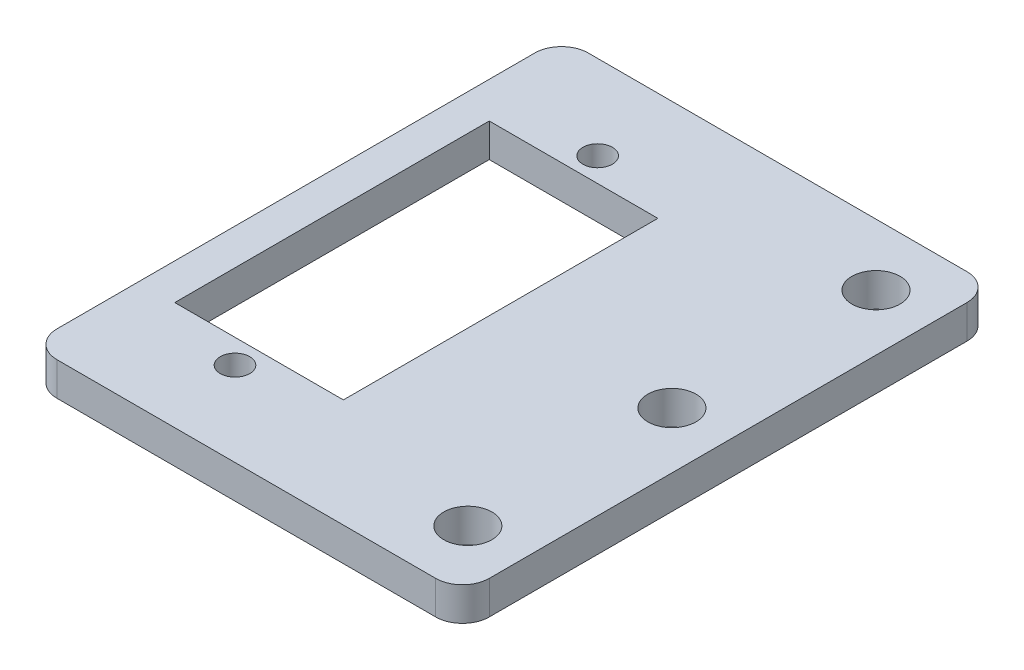
SolidWorks part; units mm, degrees
material "ABS PC"
ref_plane "Front Plane" through (0, 0, 0) normal (0, 0, 1) x (1, 0, 0)
ref_plane "Top Plane" through (0, 0, 0) normal (0, 1, 0) x (1, 0, 0)
ref_plane "Right Plane" through (0, 0, 0) normal (1, 0, 0) x (0, 0, -1)
sketch "Sketch1" plane through (0, 0, 0) normal (0, 1, 0) x (1, 0, 0)
  line L1 (-9, -19.85) -> (23.3, -19.85)
  line L2 (-9, -19.85) -> (-9, 19.85)
  line L3 (-9, 19.85) -> (23.3, 19.85)
  line L4 (23.3, -19.85) -> (23.3, 19.85)
  point P4 (23.3, 0)
  dimension "D1" = 32.3
  dimension "D2" = 39.7
  dimension "D3" = 9
extrude "Plate Size" add sketch "Sketch1" against normal blind 2.5
sketch "Sketch2" plane through (0, 0, 0) normal (0, 1, 0) x (1, 0, 0)
  line L1 (-6.3, -11.75) -> (6.3, -11.75)
  line L2 (-6.3, -11.75) -> (-6.3, 11.75)
  line L3 (-6.3, 11.75) -> (6.3, 11.75)
  line L4 (6.3, -11.75) -> (6.3, 11.75)
  point P4 (0, 11.75)
  point P6 (6.3, 0)
  dimension "D1" = 12.6
  dimension "D2" = 23.5
extrude "Servo Clearance" cut sketch "Sketch2" against normal through all
hole_wizard "M2 Clearance Hole1" positions "Sketch3" profile "Sketch4" hole size "M2" standard "ANSI Metric" end condition through all
sketch "Sketch3" plane through (0, 0, 0) normal (0, 1, 0) x (1, 0, 0)
  line L0 (-6.3, -11.75) -> (6.3, -11.75) construction
  line L1 (0, -13.55) -> (0, 13.55) construction
  circle A0 centre (0, -13.55) radius 1.1 construction
  circle A1 centre (0, 13.55) radius 1.1 construction
  point P0 (0, -13.55)
  point P2 (0, 13.55)
  point P21 (0, 0)
  dimension "D1" = 2.2
  dimension "D2" = 0.7
sketch "Sketch4" plane through (0, 0, 13.55) normal (1, 0, 0) x (0, 0, 1)
  line L0 (0, 0) -> (0, 2.5)
  line L1 (0, 2.5) -> (1.1, 2.5)
  line L2 (1.1, 2.5) -> (1.1, 0)
  line L5 (1.1, 0) -> (0, 0)
  line L11 (0, -6.35) -> (0, 107.95) construction
  dimension "Thru Hole Dia." = 2.2
  dimension "Thru Hole Depth" = 2.5
hole_wizard "M3 Clearance Hole1" positions "Sketch5" profile "Sketch6" hole size "M3" standard "ANSI Metric" end condition through all
sketch "Sketch5" plane through (0, 0, 0) normal (0, 1, 0) x (1, 0, 0)
  line L0 (23.3, -19.85) -> (23.3, 19.85) construction
  line L1 (19.1, -15.25) -> (19.1, 15.25) construction
  line L3 (-9, -19.85) -> (23.3, -19.85) construction
  circle A0 centre (19.1, -15.25) radius 1.8 construction
  circle A1 centre (19.1, 0) radius 1.8 construction
  circle A2 centre (19.1, 15.25) radius 1.8 construction
  point P0 (19.1, -15.25)
  point P2 (19.1, 0)
  point P4 (19.1, 15.25)
  point P24 (19.1, 0)
  dimension "D1" = 3.6
  dimension "D3" = 2.8
  dimension "D2" = 2.4
sketch "Sketch6" plane through (19.1, 0, 15.25) normal (1, 0, 0) x (0, 0, 1)
  line L0 (0, 0) -> (0, 2.5)
  line L1 (0, 2.5) -> (1.8, 2.5)
  line L2 (1.8, 2.5) -> (1.8, 0)
  line L5 (1.8, 0) -> (0, 0)
  line L11 (0, -6.35) -> (0, 107.95) construction
  dimension "Thru Hole Dia." = 3.6
  dimension "Thru Hole Depth" = 2.5
fillet "Corner Fillet1" radius 2 4 edges at (23.3, -1.25, 19.85) (23.3, -1.25, -19.85) (-9, -1.25, -19.85) (-9, -1.25, 19.85)
